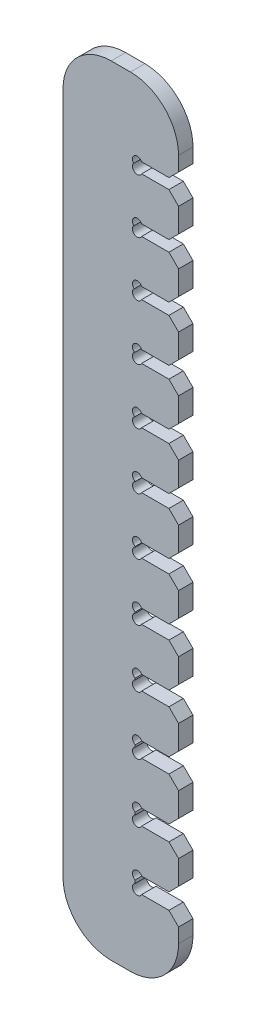
SolidWorks part; units mm, degrees
ref_plane "Front Plane" through (0, 0, 0) normal (0, 0, 1) x (1, 0, 0)
ref_plane "Top Plane" through (0, 0, 0) normal (0, 1, 0) x (1, 0, 0)
ref_plane "Right Plane" through (0, 0, 0) normal (1, 0, 0) x (0, 0, -1)
sketch "Sketch1" plane through (0, 0, 0) normal (0, 0, 1) x (1, 0, 0)
  line L0 (0, 35.4625) -> (0, -35.4625)
  line L1 (5, 40.4625) -> (7, 40.4625)
  line L2 (12, 35.4625) -> (12, 32.9625)
  line L3 (12, 32.9625) -> (7.5, 32.9625)
  line L4 (7.5, 32.9625) -> (7.5, 31.8825)
  line L5 (7.5, 31.8825) -> (12, 31.8825)
  line L6 (12, 31.8825) -> (12, 27.3825)
  line L7 (12, 27.3825) -> (7.5, 27.3825)
  line L8 (7.5, 27.3825) -> (7.5, 26.25)
  line L9 (7.5, 26.25) -> (12, 26.25)
  line L10 (12, 26.25) -> (12, 21.75)
  line L11 (12, 21.75) -> (7.5, 21.75)
  line L12 (7.5, 21.75) -> (7.5, 20.565)
  line L13 (7.5, 16.065) -> (12, 16.065)
  line L14 (12, 16.065) -> (12, 20.565)
  line L15 (12, 20.565) -> (7.5, 20.565)
  line L16 (7.5, 16.065) -> (7.5, 14.8275)
  line L17 (7.5, 14.8275) -> (12, 14.8275)
  line L18 (12, 14.8275) -> (12, 10.3275)
  line L19 (12, 10.3275) -> (7.5, 10.3275)
  line L20 (7.5, 10.3275) -> (7.5, 9.0375)
  line L21 (7.5, 9.0375) -> (12, 9.0375)
  line L22 (12, 9.0375) -> (12, 4.5375)
  line L23 (12, 4.5375) -> (7.5, 4.5375)
  line L24 (7.5, 4.5375) -> (7.5, 3.195)
  line L25 (7.5, 3.195) -> (12, 3.195)
  line L26 (12, 3.195) -> (12, -1.305)
  line L27 (12, -1.305) -> (7.5, -1.305)
  line L28 (7.5, -1.305) -> (7.5, -2.7)
  line L29 (7.5, -2.7) -> (12, -2.7)
  line L30 (12, -2.7) -> (12, -7.2)
  line L31 (12, -7.2) -> (7.5, -7.2)
  line L32 (7.5, -7.2) -> (7.5, -8.6475)
  line L33 (7.5, -8.6475) -> (12, -8.6475)
  line L34 (12, -8.6475) -> (12, -13.1475)
  line L35 (12, -13.1475) -> (7.5, -13.1475)
  line L36 (7.5, -13.1475) -> (7.5, -14.6475)
  line L37 (7.5, -14.6475) -> (12, -14.6475)
  line L38 (12, -14.6475) -> (12, -19.1475)
  line L39 (12, -19.1475) -> (7.5, -19.1475)
  line L40 (7.5, -19.1475) -> (7.5, -20.7)
  line L41 (7.5, -20.7) -> (12, -20.7)
  line L42 (12, -20.7) -> (12, -25.2)
  line L43 (12, -25.2) -> (7.5, -25.2)
  line L44 (7.5, -25.2) -> (7.5, -26.805)
  line L45 (7.5, -26.805) -> (12, -26.805)
  line L46 (12, -26.805) -> (12, -31.305)
  line L47 (12, -31.305) -> (7.5, -31.305)
  line L48 (7.5, -31.305) -> (7.5, -32.9625)
  line L49 (7.5, -32.9625) -> (12, -32.9625)
  line L50 (12, -32.9625) -> (12, -35.4625)
  line L51 (7, -40.4625) -> (5, -40.4625)
  line L53 (4, 31.4625) -> (4, -32.1337) construction
  line L54 (7.5, 31.4625) -> (4, 31.4625) construction
  line L56 (7.5, 26.8162) -> (4, 26.8162) construction
  line L58 (7.5, 20.25) -> (4, 20.25) construction
  line L60 (7.5, 15.4462) -> (4, 15.4462) construction
  line L62 (7.5, 8.8275) -> (4, 8.8275) construction
  line L64 (7.5, 3.8662) -> (4, 3.8662) construction
  line L66 (7.5, -2.805) -> (4, -2.805) construction
  line L68 (7.5, -7.9237) -> (4, -7.9237) construction
  line L70 (7.5, -13.8975) -> (4, -13.8975) construction
  line L72 (7.5, -19.9237) -> (4, -19.9237) construction
  line L74 (7.5, -26.7) -> (4, -26.7) construction
  line L76 (7.5, -32.1337) -> (4, -32.1337) construction
  arc A0 (7, 40.4625) -> (12, 35.4625) centre (7, 35.4625) cw
  arc A1 (12, -35.4625) -> (7, -40.4625) centre (7, -35.4625) cw
  arc A2 (5, -40.4625) -> (0, -35.4625) centre (5, -35.4625) cw
  arc A3 (0, 35.4625) -> (5, 40.4625) centre (5, 35.4625) cw
  point P67 (12, 40.4625)
  point P74 (0, 40.4625)
sketch "Sketch2" [suppressed] plane through (0, 0, 0) normal (0, 0, 1) x (1, 0, 0)
  line L0 (65.7671, 162.41) -> (45.76, 142.4029)
  line L1 (45.76, 136.0082) -> (66.3418, 156.59)
  line L2 (62.3519, 133.71) -> (45.76, 117.1181)
  line L3 (45.76, 110.6178) -> (62.9822, 127.84)
  line L4 (60.3771, 104.96) -> (45.76, 90.3429)
  line L5 (45.76, 85.0573) -> (59.7427, 99.04)
  line L6 (55.9122, 76.16) -> (45.76, 66.0078)
  line L7 (45.76, 59.2197) -> (56.7303, 70.19)
  line L8 (38.2877, 47.31) -> (45.76, 39.8377)
  line L9 (45.76, 32.858) -> (37.328, 41.29)
  line L10 (39.8844, 18.41) -> (45.76, 12.5344)
  line L11 (45.76, 5.4283) -> (38.8483, 12.34)
  line L12 (39.5045, -10.54) -> (45.76, -4.2845)
  line L13 (45.76, -9.5633) -> (38.6633, -16.66)
  line L14 (37.4138, -39.54) -> (45.76, -31.1938)
  line L15 (45.76, -36.8288) -> (36.8788, -45.71)
  line L16 (56.9897, -68.59) -> (45.76, -57.3603)
  line L17 (45.76, -63.2641) -> (57.3059, -74.81)
  line L18 (60.1987, -97.69) -> (45.76, -83.2513)
  line L19 (45.76, -89.3429) -> (60.3771, -103.96)
  line L20 (63.5578, -126.84) -> (45.76, -109.0422)
  line L21 (45.76, -115.2734) -> (63.6466, -133.16)
  line L22 (66.9961, -156.04) -> (45.76, -134.8039)
  line L23 (45.76, -141.1468) -> (67.0232, -162.41)
  line L24 (28.595, -161.915) -> (28.6, -161.915) construction
  line L25 (28.6, -161.915) -> (29.095, -162.41) construction
  line L26 (29.095, -162.41) -> (29.095, -162.415) construction
  line L27 (28.6, -159.225) -> (37.18, -159.225) construction
  line L28 (45.76, -125.0386) -> (37.18, -125.0386) construction
  line L29 (28.6, -130) -> (37.18, -130) construction
  line L30 (45.76, -99.1925) -> (37.18, -99.1925) construction
  line L31 (28.6, -100.825) -> (37.18, -100.825) construction
  line L32 (45.76, -73.2577) -> (37.18, -73.2577) construction
  line L33 (28.6, -71.7) -> (37.18, -71.7) construction
  line L34 (28.6, -13.6) -> (37.18, -13.6) construction
  line L35 (45.76, -47.0945) -> (37.18, -47.0945) construction
  line L36 (45.76, 0.5719) -> (37.18, 0.5719) construction
  line L37 (28.6, -42.625) -> (37.18, -42.625) construction
  line L38 (28.6, 130.775) -> (37.18, 130.775) construction
  line L39 (45.76, -20.3785) -> (37.18, -20.3785) construction
  line L40 (28.6, 15.375) -> (37.18, 15.375) construction
  line L42 (45.76, 22.6962) -> (37.18, 22.6962) construction
  line L43 (45.76, 126.5631) -> (37.18, 126.5631) construction
  line L44 (28.6, 44.3) -> (37.18, 44.3) construction
  line L46 (45.76, 49.5287) -> (37.18, 49.5287) construction
  line L47 (28.6, 159.5) -> (37.18, 159.5) construction
  line L48 (28.6, 73.175) -> (37.18, 73.175) construction
  line L50 (45.76, 75.5326) -> (37.18, 75.5326) construction
  line L52 (0, 186.01) -> (0, -186.01)
  line L53 (5, -191.01) -> (40.76, -191.01)
  line L54 (45.76, -186.01) -> (45.76, -162.41)
  line L55 (45.76, -162.41) -> (28.6, -162.41)
  line L56 (28.6, -162.41) -> (28.6, -156.04)
  line L57 (28.6, -156.04) -> (45.76, -156.04)
  line L58 (45.76, -156.04) -> (45.76, -133.16)
  line L59 (45.76, -133.16) -> (28.6, -133.16)
  line L60 (28.6, -133.16) -> (28.6, -126.84)
  line L61 (28.6, -126.84) -> (45.76, -126.84)
  line L62 (45.76, -126.84) -> (45.76, -103.96)
  line L63 (45.76, -103.96) -> (28.6, -103.96)
  line L64 (28.6, -103.96) -> (28.6, -97.69)
  line L65 (28.6, -97.69) -> (45.76, -97.69)
  line L66 (45.76, -97.69) -> (45.76, -74.81)
  line L67 (45.76, -74.81) -> (28.6, -74.81)
  line L68 (28.6, -74.81) -> (28.6, -68.59)
  line L69 (28.6, -68.59) -> (45.76, -68.59)
  line L70 (45.76, -68.59) -> (45.76, -45.71)
  line L71 (45.76, -45.71) -> (28.6, -45.71)
  line L72 (28.6, -45.71) -> (28.6, -39.54)
  line L73 (28.6, -39.54) -> (45.76, -39.54)
  line L74 (45.76, -39.54) -> (45.76, -16.66)
  line L75 (45.76, -16.66) -> (28.6, -16.66)
  line L76 (28.6, -16.66) -> (28.6, -10.54)
  line L77 (28.6, -10.54) -> (45.76, -10.54)
  line L78 (45.76, -10.54) -> (45.76, 12.34)
  line L79 (45.76, 12.34) -> (28.6, 12.34)
  line L80 (28.6, 12.34) -> (28.6, 18.41)
  line L81 (28.6, 18.41) -> (45.76, 18.41)
  line L82 (45.76, 18.41) -> (45.76, 41.29)
  line L83 (45.76, 41.29) -> (28.6, 41.29)
  line L84 (28.6, 41.29) -> (28.6, 47.31)
  line L85 (28.6, 47.31) -> (45.76, 47.31)
  line L86 (45.76, 47.31) -> (45.76, 70.19)
  line L87 (45.76, 70.19) -> (28.6, 70.19)
  line L88 (28.6, 70.19) -> (28.6, 76.16)
  line L89 (28.6, 76.16) -> (45.76, 76.16)
  line L90 (45.76, 76.16) -> (45.76, 99.04)
  line L91 (45.76, 99.04) -> (28.6, 99.04)
  line L92 (28.6, 99.04) -> (28.6, 104.96)
  line L93 (28.6, 104.96) -> (45.76, 104.96)
  line L94 (45.76, 104.96) -> (45.76, 127.84)
  line L95 (45.76, 127.84) -> (28.6, 127.84)
  line L96 (28.6, 127.84) -> (28.6, 133.71)
  line L97 (28.6, 133.71) -> (45.76, 133.71)
  line L98 (45.76, 133.71) -> (45.76, 156.59)
  line L99 (45.76, 156.59) -> (28.6, 156.59)
  line L100 (28.6, 156.59) -> (28.6, 162.41)
  line L101 (28.6, 162.41) -> (45.76, 162.41)
  line L102 (45.76, 162.41) -> (45.76, 186.01)
  line L103 (40.76, 191.01) -> (5, 191.01)
  line L104 (0, 186.01) -> (0, -186.01)
  line L105 (5, -191.01) -> (40.76, -191.01)
  line L106 (45.76, -186.01) -> (45.76, -141.1468)
  line L107 (67.0232, -162.41) -> (28.6, -162.41)
  line L108 (28.6, -162.41) -> (28.6, -156.04)
  line L109 (28.6, -156.04) -> (66.9961, -156.04)
  line L110 (45.76, -134.8039) -> (45.76, -115.2734)
  line L111 (63.6466, -133.16) -> (28.6, -133.16)
  line L112 (28.6, -133.16) -> (28.6, -126.84)
  line L113 (28.6, -126.84) -> (63.5578, -126.84)
  line L114 (45.76, -109.0422) -> (45.76, -89.3429)
  line L115 (60.3771, -103.96) -> (28.6, -103.96)
  line L116 (28.6, -103.96) -> (28.6, -97.69)
  line L117 (28.6, -97.69) -> (60.1987, -97.69)
  line L118 (45.76, -83.2513) -> (45.76, -63.2641)
  line L119 (57.3059, -74.81) -> (28.6, -74.81)
  line L120 (28.6, -74.81) -> (28.6, -68.59)
  line L121 (28.6, -68.59) -> (56.9897, -68.59)
  line L122 (45.76, -57.3603) -> (45.76, -36.8288)
  line L123 (36.8788, -45.71) -> (28.6, -45.71)
  line L124 (28.6, -45.71) -> (28.6, -39.54)
  line L125 (28.6, -39.54) -> (37.4138, -39.54)
  line L126 (45.76, -31.1938) -> (45.76, -9.5633)
  line L127 (38.6633, -16.66) -> (28.6, -16.66)
  line L128 (28.6, -16.66) -> (28.6, -10.54)
  line L129 (28.6, -10.54) -> (39.5045, -10.54)
  line L130 (45.76, -4.2845) -> (45.76, 5.4283)
  line L131 (38.8483, 12.34) -> (28.6, 12.34)
  line L132 (28.6, 12.34) -> (28.6, 18.41)
  line L133 (28.6, 18.41) -> (39.8844, 18.41)
  line L134 (45.76, 12.5344) -> (45.76, 32.858)
  line L135 (37.328, 41.29) -> (28.6, 41.29)
  line L136 (28.6, 41.29) -> (28.6, 47.31)
  line L137 (28.6, 47.31) -> (38.2877, 47.31)
  line L138 (45.76, 39.8377) -> (45.76, 59.2197)
  line L139 (56.7303, 70.19) -> (28.6, 70.19)
  line L140 (28.6, 70.19) -> (28.6, 76.16)
  line L141 (28.6, 76.16) -> (55.9122, 76.16)
  line L142 (45.76, 66.0078) -> (45.76, 85.0573)
  line L143 (59.7427, 99.04) -> (28.6, 99.04)
  line L144 (28.6, 99.04) -> (28.6, 104.96)
  line L145 (28.6, 104.96) -> (60.3771, 104.96)
  line L146 (45.76, 90.3429) -> (45.76, 110.6178)
  line L147 (62.9822, 127.84) -> (28.6, 127.84)
  line L148 (28.6, 127.84) -> (28.6, 133.71)
  line L149 (28.6, 133.71) -> (62.3519, 133.71)
  line L150 (45.76, 117.1181) -> (45.76, 136.0082)
  line L151 (66.3418, 156.59) -> (28.6, 156.59)
  line L152 (28.6, 156.59) -> (28.6, 162.41)
  line L153 (28.6, 162.41) -> (65.7671, 162.41)
  line L154 (45.76, 142.4029) -> (45.76, 186.01)
  line L155 (40.76, 191.01) -> (5, 191.01)
  line L156 (28.6, 102) -> (37.18, 102) construction
  line L158 (45.76, 100.4804) -> (37.18, 100.4804) construction
  arc A0 (28.6, -161.8443) -> (29.1657, -162.41) centre (29.095, -161.915) ccw
  arc A1 (28.6, -156.6057) -> (29.1657, -156.04) centre (29.095, -156.535) cw
  arc A2 (28.6, -93.4716) -> (29.1657, -94.0373) centre (29.095, -93.5423) ccw
  arc A3 (28.6, -166.5284) -> (29.1657, -165.9627) centre (29.095, -166.4577) cw
  arc A4 (0, -186.01) -> (5, -191.01) centre (5, -186.01) ccw
  arc A5 (40.76, -191.01) -> (45.76, -186.01) centre (40.76, -186.01) ccw
  arc A6 (45.76, 186.01) -> (40.76, 191.01) centre (40.76, 186.01) ccw
  arc A7 (5, 191.01) -> (0, 186.01) centre (5, 186.01) ccw
  arc A8 (0, -186.01) -> (5, -191.01) centre (5, -186.01) ccw
  arc A9 (40.76, -191.01) -> (45.76, -186.01) centre (40.76, -186.01) ccw
  arc A10 (45.76, 186.01) -> (40.76, 191.01) centre (40.76, 186.01) ccw
  arc A11 (5, 191.01) -> (0, 186.01) centre (5, 186.01) ccw
  arc A12 (28.6, -31.8567) -> (29.1657, -32.4224) centre (29.095, -31.9274) ccw
  arc A13 (28.6, -169.7933) -> (29.1657, -169.2276) centre (29.095, -169.7226) cw
  arc A14 (28.6, 23.2779) -> (29.1657, 22.7122) centre (29.095, 23.2072) ccw
  arc A15 (28.6, -166.6779) -> (29.1657, -166.1122) centre (29.095, -166.6072) cw
  arc A16 (28.6, 72.4888) -> (29.1657, 71.9231) centre (29.095, 72.4181) ccw
  arc A17 (28.6, -157.7388) -> (29.1657, -157.1731) centre (29.095, -157.6681) cw
  arc A18 (28.6, 116.9817) -> (29.1657, 116.416) centre (29.095, 116.911) ccw
  arc A19 (28.6, -144.1817) -> (29.1657, -143.616) centre (29.095, -144.111) cw
  arc A20 (28.6, 145.3255) -> (29.1657, 144.7598) centre (29.095, 145.2548) ccw
  arc A21 (28.6, -114.5755) -> (29.1657, -114.0098) centre (29.095, -114.5048) cw
  arc A22 (28.6, 159.9678) -> (29.1657, 159.4021) centre (29.095, 159.8971) ccw
  arc A23 (28.6, -71.3678) -> (29.1657, -70.8021) centre (29.095, -71.2971) cw
  arc A24 (28.6, 170.4253) -> (29.1657, 169.8596) centre (29.095, 170.3545) ccw
  arc A25 (28.6, -24.0753) -> (29.1657, -23.5096) centre (29.095, -24.0045) cw
  arc A26 (28.6, 175.1404) -> (29.1657, 174.5747) centre (29.095, 175.0697) ccw
  arc A27 (28.6, 28.8596) -> (29.1657, 29.4253) centre (29.095, 28.9303) cw
  arc A28 (28.6, 172.1011) -> (29.1657, 171.5354) centre (29.095, 172.0304) ccw
  arc A29 (28.6, 89.4489) -> (29.1657, 90.0146) centre (29.095, 89.5196) cw
  arc A30 (28.6, 163.6774) -> (29.1657, 163.1117) centre (29.095, 163.6067) ccw
  arc A31 (28.6, 155.3226) -> (29.1657, 155.8883) centre (29.095, 155.3933) cw
sketch "Sketch3" [suppressed] plane through (0, 0, 0) normal (0, 0, 1) x (1, 0, 0)
  line L0 (28.6, 160.91) -> (4, 160.91) construction
  line L1 (28.6, 160.91) -> (4, 160.91) construction
  line L2 (28.6, 103.46) -> (4, 103.46) construction
  line L3 (28.6, 103.46) -> (4, 103.46) construction
  line L4 (28.6, 45.81) -> (4, 45.81) construction
  line L5 (28.6, 45.81) -> (4, 45.81) construction
  line L6 (28.6, -12.04) -> (4, -12.04) construction
  line L7 (28.6, -12.04) -> (4, -12.04) construction
  line L8 (28.6, -71.7) -> (4, -71.7) construction
  line L9 (28.6, -71.7) -> (4, -71.7) construction
  line L10 (28.6, -128.34) -> (4, -128.34) construction
  line L11 (28.6, -128.34) -> (4, -128.34) construction
  line L76 (39, -136.6) -> (40, -135.6)
  line L77 (40, -135.6) -> (40, -117.6)
  line L78 (40, -117.6) -> (39, -116.6)
  line L79 (39, -116.6) -> (28.6, -133.16)
  line L80 (28.6, -133.16) -> (28.6, -126.84)
  line L81 (28.6, -126.84) -> (39, -111)
  line L82 (39, -111) -> (40, -110)
  line L83 (40, -110) -> (40, -92)
  line L84 (40, -92) -> (39, -91)
  line L85 (39, -91) -> (28.6, -103.96)
  line L86 (28.6, -103.96) -> (28.6, -97.69)
  line L87 (28.6, -97.69) -> (39, -85.45)
  line L88 (39, -85.45) -> (40, -84.45)
  line L89 (40, -84.45) -> (40, -66.45)
  line L90 (40, -66.45) -> (39, -65.45)
  line L91 (39, -65.45) -> (28.6, -74.81)
  line L92 (28.6, -74.81) -> (28.6, -68.59)
  line L93 (28.6, -68.59) -> (39, -59.95)
  line L94 (39, -59.95) -> (40, -58.95)
  line L95 (40, -58.95) -> (40, -40.95)
  line L96 (40, -40.95) -> (39, -39.95)
  line L97 (39, -39.95) -> (28.6, -45.71)
  line L98 (28.6, -45.71) -> (28.6, -39.54)
  line L99 (28.6, -39.54) -> (39, -34.5)
  line L100 (39, -34.5) -> (40, -33.5)
  line L101 (40, -33.5) -> (40, -15.5)
  line L102 (40, -15.5) -> (39, -14.5)
  line L103 (39, -14.5) -> (28.6, -16.66)
  line L104 (28.6, -16.66) -> (28.6, -10.54)
  line L105 (28.6, -10.54) -> (39, -9.1)
  line L106 (39, -9.1) -> (40, -8.1)
  line L107 (40, -8.1) -> (40, 9.9)
  line L108 (40, 9.9) -> (39, 10.9)
  line L109 (39, 10.9) -> (28.6, 12.34)
  line L110 (28.6, 12.34) -> (28.6, 18.41)
  line L111 (28.6, 18.41) -> (39, 16.25)
  line L112 (39, 16.25) -> (40, 17.25)
  line L113 (40, 17.25) -> (40, 35.25)
  line L114 (40, 35.25) -> (39, 36.25)
  line L115 (39, 36.25) -> (28.6, 41.29)
  line L116 (28.6, 41.29) -> (28.6, 47.31)
  line L117 (28.6, 47.31) -> (39, 41.55)
  line L118 (39, 41.55) -> (40, 42.55)
  line L119 (40, 42.55) -> (40, 60.55)
  line L120 (40, 60.55) -> (39, 61.55)
  line L121 (39, 61.55) -> (28.6, 70.19)
  line L122 (28.6, 70.19) -> (28.6, 76.16)
  line L123 (28.6, 76.16) -> (39, 66.8)
  line L124 (39, 66.8) -> (40, 67.8)
  line L125 (40, 67.8) -> (40, 85.8)
  line L126 (40, 85.8) -> (39, 86.8)
  line L127 (39, 86.8) -> (28.6, 99.04)
  line L128 (28.6, 99.04) -> (28.6, 104.96)
  line L129 (28.6, 104.96) -> (39, 92)
  line L130 (39, 92) -> (40, 93)
  line L131 (40, 93) -> (40, 111)
  line L132 (40, 111) -> (39, 112)
  line L133 (39, 112) -> (28.6, 127.84)
  line L134 (28.6, 127.84) -> (28.6, 133.71)
  line L135 (28.6, 133.71) -> (39, 117.15)
  line L136 (39, 117.15) -> (40, 118.15)
  line L137 (40, 118.15) -> (40, 136.15)
  line L138 (40, 136.15) -> (39, 137.15)
  line L139 (39, 137.15) -> (28.6, 156.59)
  line L140 (28.6, 156.59) -> (28.6, 162.41)
  line L141 (28.6, 162.41) -> (39, 142.25)
  line L142 (39, 142.25) -> (40, 143.25)
  line L143 (40, 143.25) -> (45.76, 186.01)
  line L144 (40.76, 191.01) -> (5, 191.01)
  line L145 (0, 186.01) -> (0, -186.01)
  line L146 (5, -191.01) -> (40.76, -191.01)
  line L147 (45.76, -186.01) -> (40, -143.25)
  line L148 (40, -143.25) -> (39, -142.25)
  line L149 (39, -142.25) -> (28.6, -162.41)
  line L150 (28.6, -162.41) -> (28.6, -156.04)
  line L151 (28.6, -156.04) -> (39, -136.6)
  line L152 (39, -136.6) -> (40, -135.6)
  line L153 (40, -135.6) -> (40, -117.6)
  line L154 (40, -117.6) -> (39, -116.6)
  line L155 (39, -116.6) -> (25.6649, -116.6)
  line L156 (25, -115.9351) -> (25, -111.6649)
  line L157 (25.6649, -111) -> (39, -111)
  line L158 (39, -111) -> (40, -110)
  line L159 (40, -110) -> (40, -92)
  line L160 (40, -92) -> (39, -91)
  line L161 (39, -91) -> (25.6649, -91)
  line L162 (25, -90.3351) -> (25, -86.1149)
  line L163 (25.6649, -85.45) -> (39, -85.45)
  line L164 (39, -85.45) -> (40, -84.45)
  line L165 (40, -84.45) -> (40, -66.45)
  line L166 (40, -66.45) -> (39, -65.45)
  line L167 (39, -65.45) -> (25.6649, -65.45)
  line L168 (25, -64.7851) -> (25, -60.6149)
  line L169 (25.6649, -59.95) -> (39, -59.95)
  line L170 (39, -59.95) -> (40, -58.95)
  line L171 (40, -58.95) -> (40, -40.95)
  line L172 (40, -40.95) -> (39, -39.95)
  line L173 (39, -39.95) -> (25.6649, -39.95)
  line L174 (25, -39.2851) -> (25, -35.1649)
  line L175 (25.6649, -34.5) -> (39, -34.5)
  line L176 (39, -34.5) -> (40, -33.5)
  line L177 (40, -33.5) -> (40, -15.5)
  line L178 (40, -15.5) -> (39, -14.5)
  line L179 (39, -14.5) -> (25.6649, -14.5)
  line L180 (25, -13.8351) -> (25, -9.7649)
  line L181 (25.6649, -9.1) -> (39, -9.1)
  line L182 (39, -9.1) -> (40, -8.1)
  line L183 (40, -8.1) -> (40, 9.9)
  line L184 (40, 9.9) -> (39, 10.9)
  line L185 (39, 10.9) -> (25.6649, 10.9)
  line L186 (25, 11.5649) -> (25, 15.5851)
  line L187 (25.6649, 16.25) -> (39, 16.25)
  line L188 (39, 16.25) -> (40, 17.25)
  line L189 (40, 17.25) -> (40, 35.25)
  line L190 (40, 35.25) -> (39, 36.25)
  line L191 (39, 36.25) -> (25.6649, 36.25)
  line L192 (25, 36.9149) -> (25, 40.8851)
  line L193 (25.6649, 41.55) -> (39, 41.55)
  line L194 (39, 41.55) -> (40, 42.55)
  line L195 (40, 42.55) -> (40, 60.55)
  line L196 (40, 60.55) -> (39, 61.55)
  line L197 (39, 61.55) -> (25.6649, 61.55)
  line L198 (25, 62.2149) -> (25, 66.1351)
  line L199 (25.6649, 66.8) -> (39, 66.8)
  line L200 (39, 66.8) -> (40, 67.8)
  line L201 (40, 67.8) -> (40, 85.8)
  line L202 (40, 85.8) -> (39, 86.8)
  line L203 (39, 86.8) -> (25.6649, 86.8)
  line L204 (25, 87.4649) -> (25, 91.3351)
  line L205 (25.6649, 92) -> (39, 92)
  line L206 (39, 92) -> (40, 93)
  line L207 (40, 93) -> (40, 111)
  line L208 (40, 111) -> (39, 112)
  line L209 (39, 112) -> (25.6649, 112)
  line L210 (25, 112.6649) -> (25, 116.4851)
  line L211 (25.6649, 117.15) -> (39, 117.15)
  line L212 (39, 117.15) -> (40, 118.15)
  line L213 (40, 118.15) -> (40, 136.15)
  line L214 (40, 136.15) -> (39, 137.15)
  line L215 (39, 137.15) -> (25.6649, 137.15)
  line L216 (25, 137.8149) -> (25, 141.5851)
  line L217 (25.6649, 142.25) -> (39, 142.25)
  line L218 (39, 142.25) -> (40, 143.25)
  line L219 (40, 143.25) -> (45.76, 186.01)
  line L220 (40.76, 191.01) -> (5, 191.01)
  line L221 (0, 186.01) -> (0, -186.01)
  line L222 (5, -191.01) -> (40.76, -191.01)
  line L223 (45.76, -186.01) -> (40, -143.25)
  line L224 (40, -143.25) -> (39, -142.25)
  line L225 (39, -142.25) -> (25.6649, -142.25)
  line L226 (25, -141.5851) -> (25, -137.2649)
  line L227 (25.6649, -136.6) -> (39, -136.6)
  arc A0 (25, -115.9351) -> (25.6649, -116.6) centre (25.2121, -116.3879) ccw construction
  arc A1 (25.6649, -136.6) -> (25, -137.2649) centre (25.2121, -136.8121) ccw construction
  arc A2 (25, -141.5851) -> (25.6649, -142.25) centre (25.2121, -142.0379) ccw construction
  arc A3 (25, -64.7851) -> (25.6649, -65.45) centre (25.2121, -65.2379) ccw construction
  arc A4 (45.76, 186.01) -> (40.76, 191.01) centre (40.76, 186.01) ccw
  arc A5 (5, 191.01) -> (0, 186.01) centre (5, 186.01) ccw
  arc A6 (0, -186.01) -> (5, -191.01) centre (5, -186.01) ccw
  arc A7 (40.76, -191.01) -> (45.76, -186.01) centre (40.76, -186.01) ccw
  arc A8 (45.76, 186.01) -> (40.76, 191.01) centre (40.76, 186.01) ccw
  arc A9 (5, 191.01) -> (0, 186.01) centre (5, 186.01) ccw
  arc A10 (0, -186.01) -> (5, -191.01) centre (5, -186.01) ccw
  arc A11 (40.76, -191.01) -> (45.76, -186.01) centre (40.76, -186.01) ccw
  arc A12 (25.6649, -85.45) -> (25, -86.1149) centre (25.2121, -85.6621) ccw construction
  arc A13 (25, -90.3351) -> (25.6649, -91) centre (25.2121, -90.7879) ccw construction
  arc A14 (25.6649, -111) -> (25, -111.6649) centre (25.2121, -111.2121) ccw construction
  arc A15 (25, -39.2851) -> (25.6649, -39.95) centre (25.2121, -39.7379) ccw construction
  arc A16 (25.6649, -59.95) -> (25, -60.6149) centre (25.2121, -60.1621) ccw construction
  arc A17 (25, -13.8351) -> (25.6649, -14.5) centre (25.2121, -14.2879) ccw construction
  arc A18 (25.6649, -34.5) -> (25, -35.1649) centre (25.2121, -34.7121) ccw construction
  arc A19 (25, 11.5649) -> (25.6649, 10.9) centre (25.2121, 11.1121) ccw construction
  arc A20 (25.6649, -9.1) -> (25, -9.7649) centre (25.2121, -9.3121) ccw construction
  arc A21 (25.6649, 66.8) -> (25, 66.1351) centre (25.2121, 66.5879) ccw construction
  arc A22 (25, 62.2149) -> (25.6649, 61.55) centre (25.2121, 61.7621) ccw construction
  arc A23 (25.6649, 41.55) -> (25, 40.8851) centre (25.2121, 41.3379) ccw construction
  arc A24 (25, 36.9149) -> (25.6649, 36.25) centre (25.2121, 36.4621) ccw construction
  arc A25 (25.6649, 16.25) -> (25, 15.5851) centre (25.2121, 16.0379) ccw construction
  arc A26 (25.6649, 117.15) -> (25, 116.4851) centre (25.2121, 116.9379) ccw construction
  arc A27 (25, 112.6649) -> (25.6649, 112) centre (25.2121, 112.2121) ccw construction
  arc A28 (25.6649, 92) -> (25, 91.3351) centre (25.2121, 91.7879) ccw construction
  arc A29 (25, 87.4649) -> (25.6649, 86.8) centre (25.2121, 87.0121) ccw construction
  arc A30 (25.6649, 142.25) -> (25, 141.5851) centre (25.2121, 142.0379) ccw construction
  arc A31 (25, 137.8149) -> (25.6649, 137.15) centre (25.2121, 137.3621) ccw construction
  arc A32 (25, -115.9351) -> (25.6649, -116.6) centre (25.2121, -116.3879) ccw
  arc A33 (25.6649, -136.6) -> (25, -137.2649) centre (25.2121, -136.8121) ccw
  arc A34 (25, -141.5851) -> (25.6649, -142.25) centre (25.2121, -142.0379) ccw
  arc A35 (25, -64.7851) -> (25.6649, -65.45) centre (25.2121, -65.2379) ccw
  arc A36 (25.6649, -85.45) -> (25, -86.1149) centre (25.2121, -85.6621) ccw
  arc A37 (25, -90.3351) -> (25.6649, -91) centre (25.2121, -90.7879) ccw
  arc A38 (25.6649, -111) -> (25, -111.6649) centre (25.2121, -111.2121) ccw
  arc A39 (25, -39.2851) -> (25.6649, -39.95) centre (25.2121, -39.7379) ccw
  arc A40 (25.6649, -59.95) -> (25, -60.6149) centre (25.2121, -60.1621) ccw
  arc A41 (25, -13.8351) -> (25.6649, -14.5) centre (25.2121, -14.2879) ccw
  arc A42 (25.6649, -34.5) -> (25, -35.1649) centre (25.2121, -34.7121) ccw
  arc A43 (25, 11.5649) -> (25.6649, 10.9) centre (25.2121, 11.1121) ccw
  arc A44 (25.6649, -9.1) -> (25, -9.7649) centre (25.2121, -9.3121) ccw
  arc A45 (25.6649, 66.8) -> (25, 66.1351) centre (25.2121, 66.5879) ccw
  arc A46 (25, 62.2149) -> (25.6649, 61.55) centre (25.2121, 61.7621) ccw
  arc A47 (25.6649, 41.55) -> (25, 40.8851) centre (25.2121, 41.3379) ccw
  arc A48 (25, 36.9149) -> (25.6649, 36.25) centre (25.2121, 36.4621) ccw
  arc A49 (25.6649, 16.25) -> (25, 15.5851) centre (25.2121, 16.0379) ccw
  arc A50 (25.6649, 117.15) -> (25, 116.4851) centre (25.2121, 116.9379) ccw
  arc A51 (25, 112.6649) -> (25.6649, 112) centre (25.2121, 112.2121) ccw
  arc A52 (25.6649, 92) -> (25, 91.3351) centre (25.2121, 91.7879) ccw
  arc A53 (25, 87.4649) -> (25.6649, 86.8) centre (25.2121, 87.0121) ccw
  arc A54 (25.6649, 142.25) -> (25, 141.5851) centre (25.2121, 142.0379) ccw
  arc A55 (25, 137.8149) -> (25.6649, 137.15) centre (25.2121, 137.3621) ccw
  text T0 "Thickness\r\n+1/2 Kerf\r\n" font "Century Gothic" height 2.5
  text T1 "Thickness\r\n+ Kerf\r\n" font "Century Gothic" height 2.5
  text T2 "Thickness\r\n+3/2 Kerf\r\n" font "Century Gothic" height 2.5
  text T3 "Thickness\r\n+2 Kerf\r\n" font "Century Gothic" height 2.5
  text T4 "Thickness\r\n+5/2 Kerf\r\n" font "Century Gothic" height 2.5
  text T5 "Thickness\r\n+3 Kerf\r\n" font "Century Gothic" height 2.5
  dimension "D1" = 0
extrude "Boss-Extrude1" add sketch "Sketch1" along normal blind 1.5
chamfer "Chamfer1" distance 1 angle 45 24 edges at (12, -32.9625, 0.75) (12, -31.305, 0.75) (12, -26.805, 0.75) (12, -25.2, 0.75) (12, -20.7, 0.75) (12, -19.1475, 0.75) (12, -14.6475, 0.75) (12, -13.1475, 0.75) (12, -8.6475, 0.75) (12, -7.2, 0.75) (12, -2.7, 0.75) (12, -1.305, 0.75) (12, 3.195, 0.75) (12, 4.5375, 0.75) (12, 9.0375, 0.75) (12, 10.3275, 0.75) (12, 14.8275, 0.75) (12, 16.065, 0.75) (12, 20.565, 0.75) (12, 21.75, 0.75) (12, 26.25, 0.75) (12, 27.3825, 0.75) (12, 32.9625, 0.75) (12, 31.8825, 0.75)
hole_wizard "Ø1.0mm Dowel Hole1" positions "Sketch4" profile "Sketch5" hole size "Ø1.0" standard "ISO" end condition through all
sketch "Sketch4" plane through (0, 0, 1.5) normal (0, 0, 1) x (1, 0, 0)
  line L0 (7.7121, 40.4625) -> (7.7121, -40.4625) construction
  line L1 (7, 40.4625) -> (5, 40.4625) construction
  line L2 (5, -40.4625) -> (7, -40.4625) construction
  line L3 (7.7121, -32.7504) -> (12, -32.7504) construction
  line L4 (12, -35.4625) -> (12, -33.9625) construction
  line L5 (9.25, -32.9625) -> (9.25, -32.7504) construction
  line L6 (11, -32.9625) -> (7.5, -32.9625) construction
  line L8 (7.5, -32.9625) -> (7.5, -31.305) construction
  line L9 (7.5, -32.1337) -> (7.7121, -32.1337) construction
  line L11 (12, -29.055) -> (7.7121, -29.055) construction
  line L12 (12, -30.305) -> (12, -27.805) construction
  line L14 (7.5, -26.0025) -> (7.7121, -26.0025) construction
  line L15 (7.5, -26.805) -> (7.5, -25.2) construction
  line L17 (12, -22.95) -> (7.7121, -22.95) construction
  line L18 (12, -24.2) -> (12, -21.7) construction
  line L20 (12, -16.8975) -> (7.7121, -16.8975) construction
  line L21 (12, -18.1475) -> (12, -15.6475) construction
  line L23 (7.5, -19.9237) -> (7.7121, -19.9237) construction
  line L24 (7.5, -20.7) -> (7.5, -19.1475) construction
  line L27 (7.5, -13.8975) -> (7.7121, -13.8975) construction
  line L28 (7.5, -14.6475) -> (7.5, -13.1475) construction
  line L30 (12, -10.8975) -> (7.7121, -10.8975) construction
  line L31 (12, -12.1475) -> (12, -9.6475) construction
  line L33 (7.5, -7.9237) -> (7.7121, -7.9237) construction
  line L34 (7.5, -8.6475) -> (7.5, -7.2) construction
  line L36 (12, -4.95) -> (7.7121, -4.95) construction
  line L37 (12, -6.2) -> (12, -3.7) construction
  line L40 (7.5, -2.0025) -> (7.7121, -2.0025) construction
  line L41 (7.5, -2.7) -> (7.5, -1.305) construction
  line L43 (12, 0.945) -> (7.7121, 0.945) construction
  line L44 (12, -0.305) -> (12, 2.195) construction
  line L46 (7.5, 3.8662) -> (7.7121, 3.8663) construction
  line L47 (7.5, 3.195) -> (7.5, 4.5375) construction
  line L49 (12, 6.7875) -> (7.7121, 6.7875) construction
  line L50 (12, 5.5375) -> (12, 8.0375) construction
  line L52 (7.5, 9.6825) -> (7.7121, 9.6825) construction
  line L53 (7.5, 9.0375) -> (7.5, 10.3275) construction
  line L55 (12, 12.5775) -> (7.7121, 12.5775) construction
  line L56 (12, 11.3275) -> (12, 13.8275) construction
  line L58 (7.5, 15.4462) -> (7.7121, 15.4462) construction
  line L59 (7.5, 14.8275) -> (7.5, 16.065) construction
  line L61 (12, 18.315) -> (7.7121, 18.315) construction
  line L62 (12, 17.065) -> (12, 19.565) construction
  line L64 (7.5, 21.1575) -> (7.7121, 21.1575) construction
  line L65 (7.5, 20.565) -> (7.5, 21.75) construction
  line L67 (12, 24) -> (7.7121, 24) construction
  line L68 (12, 22.75) -> (12, 25.25) construction
  line L70 (7.5, 26.8162) -> (7.7121, 26.8162) construction
  line L71 (7.5, 26.25) -> (7.5, 27.3825) construction
  line L73 (12, 29.6325) -> (7.7121, 29.6325) construction
  line L74 (12, 28.3825) -> (12, 30.8825) construction
  line L76 (7.5, 32.4225) -> (7.7121, 32.4225) construction
  line L77 (7.5, 31.8825) -> (7.5, 32.9625) construction
  point P0 (7.7121, 32.7504)
  point P2 (7.7121, 32.0946)
  point P4 (7.7121, 27.1704)
  point P6 (7.7121, 26.4621)
  point P8 (7.7121, 21.5379)
  point P10 (7.7121, 20.7771)
  point P12 (7.7121, 15.8529)
  point P14 (7.7121, 15.0396)
  point P16 (7.7121, 10.1154)
  point P18 (7.7121, 9.2496)
  point P20 (7.7121, 4.3254)
  point P22 (7.7121, 3.4071)
  point P24 (7.7121, -1.5171)
  point P26 (7.7121, -2.4879)
  point P28 (7.7121, -7.4121)
  point P30 (7.7121, -8.4354)
  point P32 (7.7121, -13.3596)
  point P34 (7.7121, -14.4354)
  point P36 (7.7121, -19.3596)
  point P38 (7.7121, -20.4879)
  point P40 (7.7121, -25.4121)
  point P42 (7.7121, -26.5929)
  point P44 (7.7121, -31.5171)
  point P46 (7.7121, -32.7504)
  dimension "D1" = 0.3
sketch "Sketch5" plane through (7.7121, 32.7504, 1.5) normal (1, 0, 0) x (0, -1, 0)
  line L0 (0, 0) -> (0, 1.5)
  line L1 (0, 1.5) -> (0.5, 1.5)
  line L2 (0.5, 1.5) -> (0.5, 0)
  line L5 (0.5, 0) -> (0, 0)
  line L11 (0, -6.35) -> (0, 107.95) construction
  dimension "Thru Hole Dia." = 1
  dimension "Thru Hole Depth" = 1.5
equation "\"Mat_Thickness\" = 1.5mm"
equation "\"Kerf\"= 0.21mm"
equation "\"D1@Sketch1\"=\"Mat_Thickness\"*5"
equation "\"D3@Sketch1\"=\"Mat_Thickness\"*3"
equation "\"D2@Sketch1\"=\"Mat_Thickness\"*8"
equation "\"D4@Sketch1\"=\"Mat_Thickness\"-\"Kerf\"*8/4"
equation "\"D5@Sketch1\"=\"Mat_Thickness\"-\"Kerf\"*7/4"
equation "\"D6@Sketch1\"=\"Mat_Thickness\"*3"
equation "\"D7@Sketch1\"=\"Mat_Thickness\"-\"Kerf\"*6/4"
equation "\"D8@Sketch1\"=\"Mat_Thickness\"-\"Kerf\"*5/4"
equation "\"D9@Sketch1\"=\"Mat_Thickness\"-\"Kerf\""
equation "\"D10@Sketch1\"=\"Mat_Thickness\"-\"Kerf\"*3/4"
equation "\"D11@Sketch1\"=\"Mat_Thickness\"-\"Kerf\"*2/4"
equation "\"D12@Sketch1\"=\"Mat_Thickness\"-\"Kerf\"*1/4"
equation "\"D13@Sketch1\"=\"Mat_Thickness\""
equation "\"D14@Sketch1\"=\"Mat_Thickness\"+\"Kerf\"*1/4"
equation "\"D15@Sketch1\"=\"Mat_Thickness\"+\"Kerf\"*2/4"
equation "\"D16@Sketch1\"=\"Mat_Thickness\"+\"Kerf\"*3/4"
equation "\"D3@Sketch2\"=\"Kerf\""
equation "\"D1@Boss-Extrude1\"=\"Mat_Thickness\""
